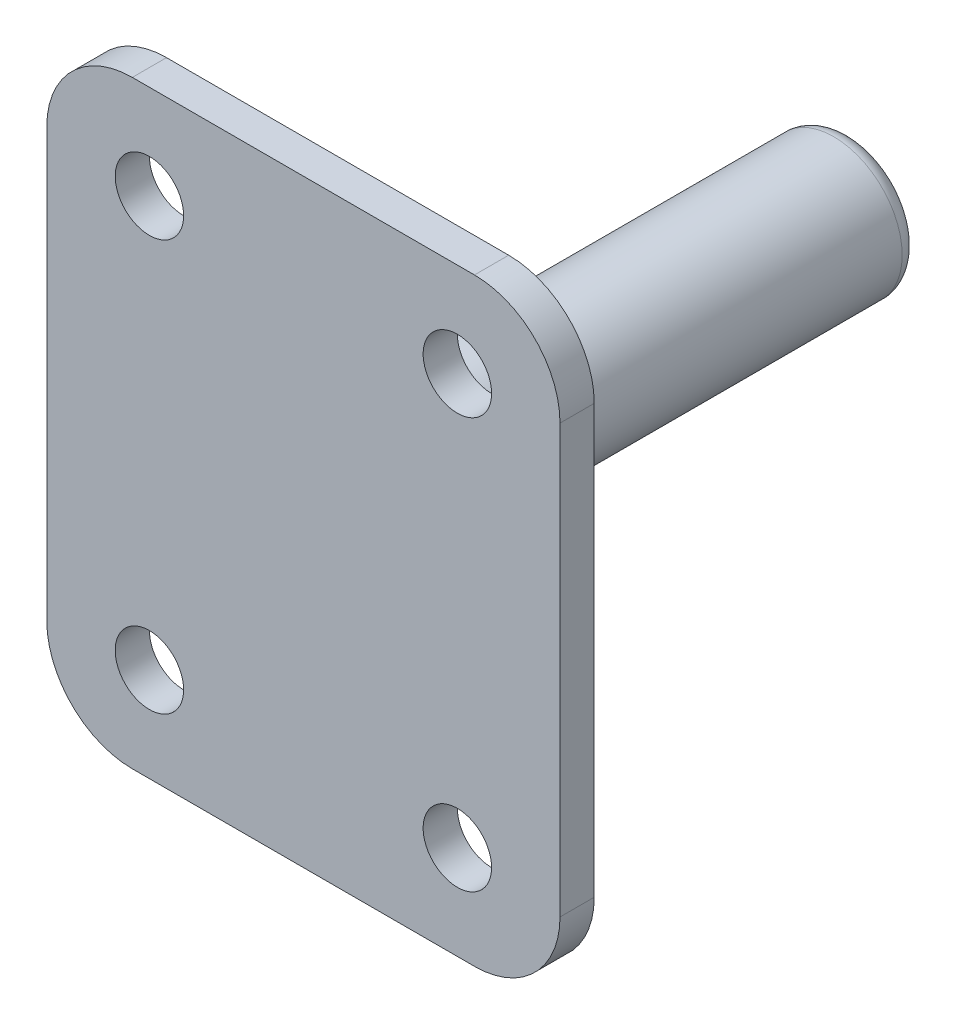
SolidWorks part; units mm, degrees
material "Plain Carbon Steel"
ref_plane "Front Plane" through (0, 0, 0) normal (0, 0, 1) x (1, 0, 0)
ref_plane "Top Plane" through (0, 0, 0) normal (0, 1, 0) x (1, 0, 0)
ref_plane "Right Plane" through (0, 0, 0) normal (1, 0, 0) x (0, 0, -1)
sketch "Sketch2" plane through (0, 0, 0) normal (0, 0, 1) x (1, 0, 0)
  line L0 (0, 0) -> (30, 0)
  line L1 (0, 0) -> (0, -35)
  line L2 (30, 0) -> (30, -35)
  line L3 (0, -35) -> (30, -35)
  line L4 (0, -17.5) -> (30, -17.5) construction
  line L5 (15, 0) -> (15, -35) construction
  dimension "D1" = 30
  dimension "D2" = 35
extrude "Boss-Extrude1" add sketch "Sketch2" along normal blind 2
fillet "Fillet1" radius 5 4 edges at (0, -35, 1) (30, -35, 1) (30, 0, 1) (0, 0, 1)
sketch "Sketch3" plane through (0, 0, 2) normal (0, 0, 1) x (1, 0, 0)
  line L0 (0, -17.5) -> (30, -17.5) construction
  line L1 (0, -5) -> (0, -30) construction
  line L2 (30, -30) -> (30, -5) construction
  line L4 (6, -5.5) -> (24, -5.5) construction
  line L5 (6, -5.5) -> (6, -29.5) construction
  line L6 (24, -5.5) -> (24, -29.5) construction
  line L7 (6, -29.5) -> (24, -29.5) construction
  circle A4 centre (6, -5.5) radius 2
  circle A5 centre (24, -5.5) radius 2
  circle A6 centre (6, -29.5) radius 2
  circle A7 centre (24, -29.5) radius 2
  point P2 (15, -5.5)
  point P5 (15, -17.5)
  point P16 (30, -17.5)
  point P17 (24, -17.5)
  dimension "D1" = 4
  dimension "D2" = 24
  dimension "D3" = 18
extrude "Cut-Extrude1" cut sketch "Sketch3" against normal blind 10
sketch "Sketch6" plane through (0, 0, 0) normal (0, 0, -1) x (-1, 0, 0)
  line L0 (-30, -17.5) -> (0, -17.5) construction
  line L1 (-30, -30) -> (-30, -5) construction
  line L3 (0, -5) -> (0, -30) construction
  circle A0 centre (-15, -17.5) radius 4
  point P2 (-15, -17.5)
  dimension "D1" = 8
extrude "Boss-Extrude2" add sketch "Sketch6" along normal blind 30
fillet "Fillet2" radius 1 1 edges at (11, -17.5, -30)
